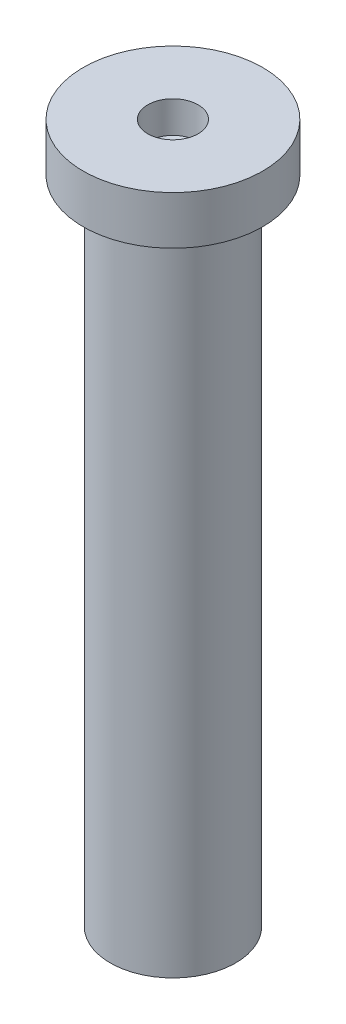
SolidWorks part; units mm, degrees
ref_plane "Front Plane" through (0, 0, 0) normal (0, 0, 1) x (1, 0, 0)
ref_plane "Top Plane" through (0, 0, 0) normal (0, 1, 0) x (1, 0, 0)
ref_plane "Right Plane" through (0, 0, 0) normal (1, 0, 0) x (0, 0, -1)
sketch "Sketch1" plane through (0, 0, 0) normal (0, 0, 1) x (1, 0, 0)
  line L0 (0.5219, 12.9427) -> (0.5219, 12.2842)
  line L1 (0, -1.5573) -> (1.3, -1.5573)
  line L2 (1.3, -1.5573) -> (1.3, 11.9427)
  line L3 (1.3, 11.9427) -> (1.8614, 11.9427)
  line L4 (1.8614, 11.9427) -> (1.8614, 12.9427)
  line L5 (1.8614, 12.9427) -> (0.5219, 12.9427)
  line L7 (0, -1.5573) -> (0, 11.8188)
  line L8 (0.5219, 12.2842) -> (0, 11.8188)
  point P1 (0, 12.0879)
  point P9 (0.5219, 12.2842)
  point P10 (0, 11.8188)
  dimension "D2" = 13.5
  dimension "D3" = 1
revolve "Revolve1" add sketch "Sketch1" angle 360 about L7
